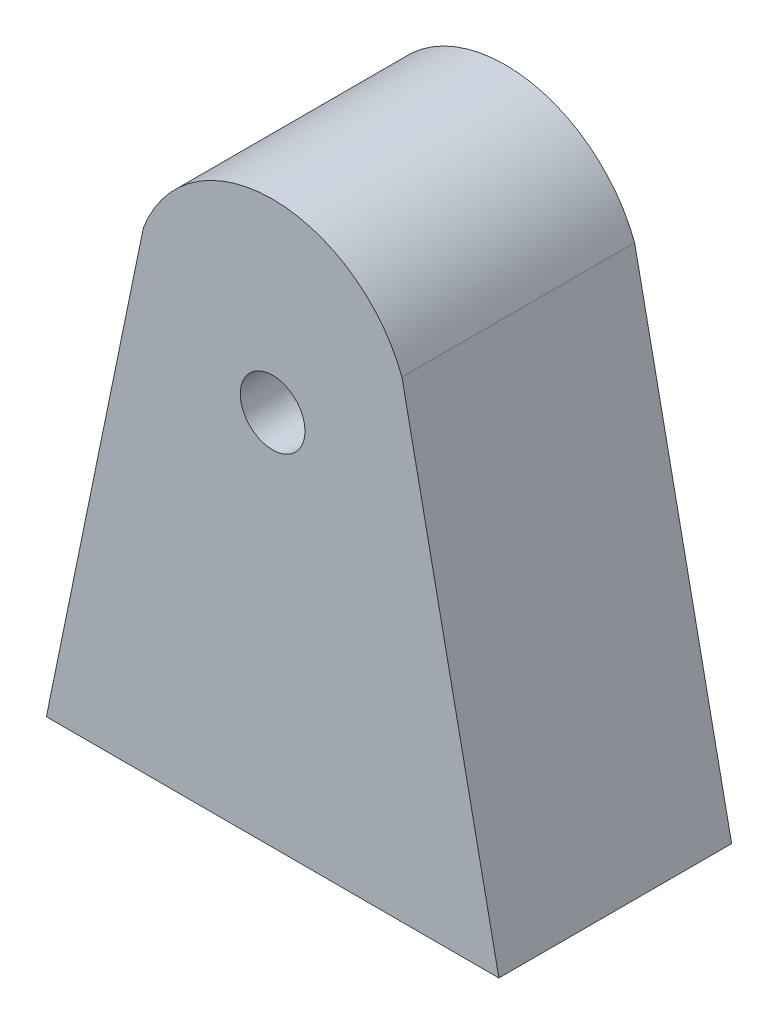
SolidWorks part; units mm, degrees
ref_plane "Front Plane" through (0, 0, 0) normal (0, 0, 1) x (1, 0, 0)
ref_plane "Top Plane" through (0, 0, 0) normal (0, 1, 0) x (1, 0, 0)
ref_plane "Right Plane" through (0, 0, 0) normal (1, 0, 0) x (0, 0, -1)
sketch "Sketch1" plane through (0, 0, 0) normal (0, 0, 1) x (1, 0, 0)
  line L0 (0, 0) -> (50.8, 0) construction
  line L1 (0, 0) -> (-19.05, -92.71)
  line L2 (69.85, -92.71) -> (-19.05, -92.71)
  line L3 (25.4, -92.71) -> (25.4, 0) construction
  line L4 (50.8, 0) -> (69.85, -92.71)
  line L6 (25.4, 0) -> (25.4, 17.5651) construction
  arc A0 (0, 0) -> (50.8, 0) centre (25.4, -9.5823) cw
  dimension "D1" = 50.8
  dimension "D2" = 44.45
  dimension "D3" = 92.71
  dimension "D4" = 92.71
  dimension "D5" = 44.45
extrude "Boss-Extrude1" add sketch "Sketch1" along normal blind 45.72
shell "Shell1" thickness 2.54
sketch "Sketch2" plane through (0, 0, 35.56) normal (0, 0, -1) x (-1, 0, 0)
  line L0 (-25.4, 17.5651) -> (-25.4, -18.7381)
  arc A0 (0, 0) -> (-50.8, 0) centre (-25.4, -9.5823) ccw construction
extrude "Boss-Extrude2" add sketch "Sketch2" along normal blind 5.08
sketch "Sketch3" plane through (0, 0, 0) normal (0, 0, -1) x (-1, 0, 0)
  circle A0 centre (-25.4, -18.7381) radius 6.35
  dimension "D1" = 12.7
sketch "Sketch4" plane through (2.488, -0.5112, 0) normal (0.9795, -0.2013, 0) x (0, 0, -1)
  line L0 (-10.16, -0.2062) -> (-10.16, -94.125) construction
  line L1 (-17.78, -44.3323) -> (-22.86, -44.3323)
  line L2 (-17.78, -44.3323) -> (-17.78, -46.8723)
  line L3 (-17.78, -46.8723) -> (-22.86, -46.8723)
  line L4 (-22.86, -44.3323) -> (-22.86, -46.8723)
  line L5 (-30.48, -94.125) -> (-30.48, -0.2062) construction
  dimension "D1" = 7.62
  dimension "D2" = 2.54
  dimension "D3" = 5.08
  dimension "D4" = 7.62
extrude "Cut-Extrude1" cut sketch "Sketch3" against normal blind 45.72 contours A0
extrude "Boss-Extrude3" add sketch "Sketch4" along normal blind 5.08
sketch "Sketch5" plane through (-8.923, -43.425, 0) normal (0.2013, 0.9795, 0) x (0.9795, -0.2013, 0)
  line L0 (7.62, -17.78) -> (2.54, -17.78) construction
  line L1 (7.62, -22.86) -> (5.08, -22.86)
  line L2 (7.62, -22.86) -> (7.62, -17.78)
  line L3 (7.62, -17.78) -> (5.08, -17.78)
  line L4 (5.08, -22.86) -> (5.08, -17.78)
extrude "Boss-Extrude4" add sketch "Sketch5" along normal blind 2.54
sketch "Sketch6" plane through (4.976, -1.0225, 0) normal (-0.9795, 0.2013, 0) x (0, 0, 1)
  line L0 (22.86, -41.7923) -> (22.86, -44.3323) construction
  line L1 (17.78, -41.7923) -> (22.86, -41.7923)
  line L2 (17.78, -41.7923) -> (17.78, -43.0623)
  line L3 (17.78, -43.0623) -> (22.86, -43.0623)
  line L4 (22.86, -41.7923) -> (22.86, -43.0623)
extrude "Boss-Extrude5" add sketch "Sketch6" along normal blind 1.27
